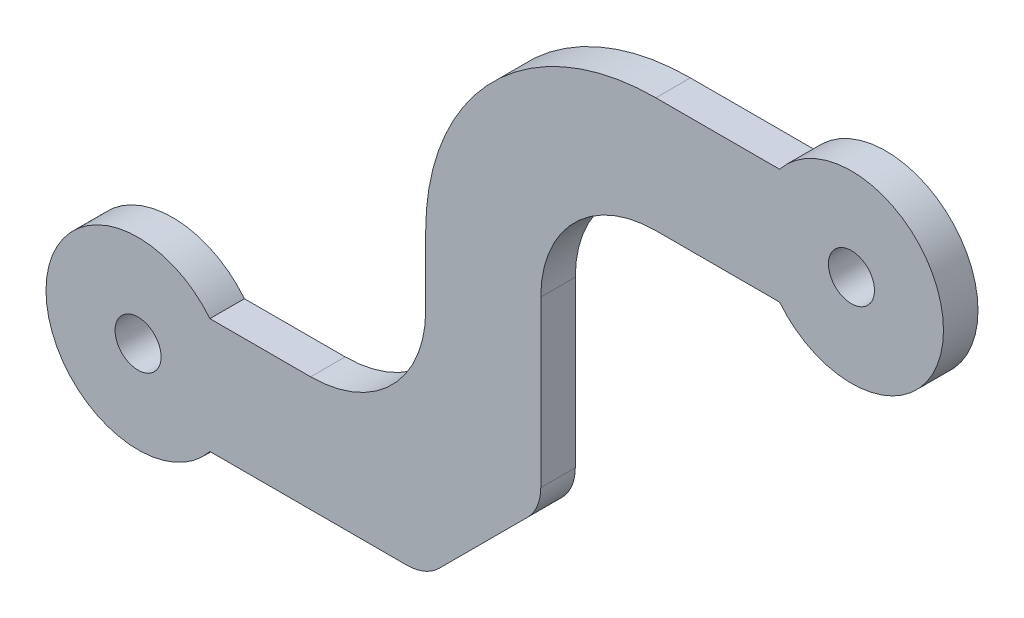
SolidWorks part; units mm, degrees
material "Galvanized Steel"
ref_plane "Front Plane" through (0, 0, 0) normal (0, 0, 1) x (1, 0, 0)
ref_plane "Top Plane" through (0, 0, 0) normal (0, 1, 0) x (1, 0, 0)
ref_plane "Right Plane" through (0, 0, 0) normal (1, 0, 0) x (0, 0, -1)
sketch "Sketch1" plane through (0, 0, 0) normal (0, 0, 1) x (1, 0, 0)
  line L1 (3.1225, 2.5) -> (12.5, 2.5)
  line L3 (3.1225, -2.5) -> (17.5, -2.5)
  line L5 (-3.9691, 0.4961) -> (17.5, -2.1875) construction
  line L6 (-3.9691, -0.4961) -> (17.5, 2.1875) construction
  line L7 (27.8775, 15.5) -> (17.5, 15.5)
  line L9 (27.8775, 20.5) -> (12.5, 20.5)
  line L11 (34.9691, 17.5039) -> (12.5, 20.3125) construction
  line L12 (34.9691, 18.4961) -> (12.5, 15.6875) construction
  line L14 (17.5, -2.5) -> (17.5, 15.5)
  line L17 (16.1645, -2.5) -> (13.8433, 20.5) construction
  line L18 (16.1567, 20.5) -> (13.8355, -2.5) construction
  line L19 (12.5, 2.5) -> (12.5, 20.5)
  circle A0 centre (0, 0) radius 1
  circle A1 centre (31, 18) radius 1
  arc A2 (3.1225, 2.5) -> (3.1225, -2.5) centre (0, 0) ccw
  arc A4 (27.8775, 15.5) -> (27.8775, 20.5) centre (31, 18) ccw
  point P15 (15, 9.0385)
  dimension "D1" = 2
  dimension "D2" = 2
  dimension "D5" = 8
  dimension "D3" = 31
  dimension "D4" = 18
  dimension "D11" = 15
extrude "Boss-Extrude1" add sketch "Sketch1" along normal blind 1.5
fillet "Fillet1" radius 10 1 edges at (12.5, 20.5, 0.75)
fillet "Fillet2" radius 5 1 edges at (17.5, 15.5, 0.75)
fillet "Fillet3" radius 5 1 edges at (12.5, 2.5, 0.75)
chamfer "Chamfer1" distance 5 angle 45 1 edges at (17.5, -2.5, 0.75)
fillet "Fillet4" radius 2 2 edges at (17.5, 2.5, 0.75) (12.5, -2.5, 0.75)
